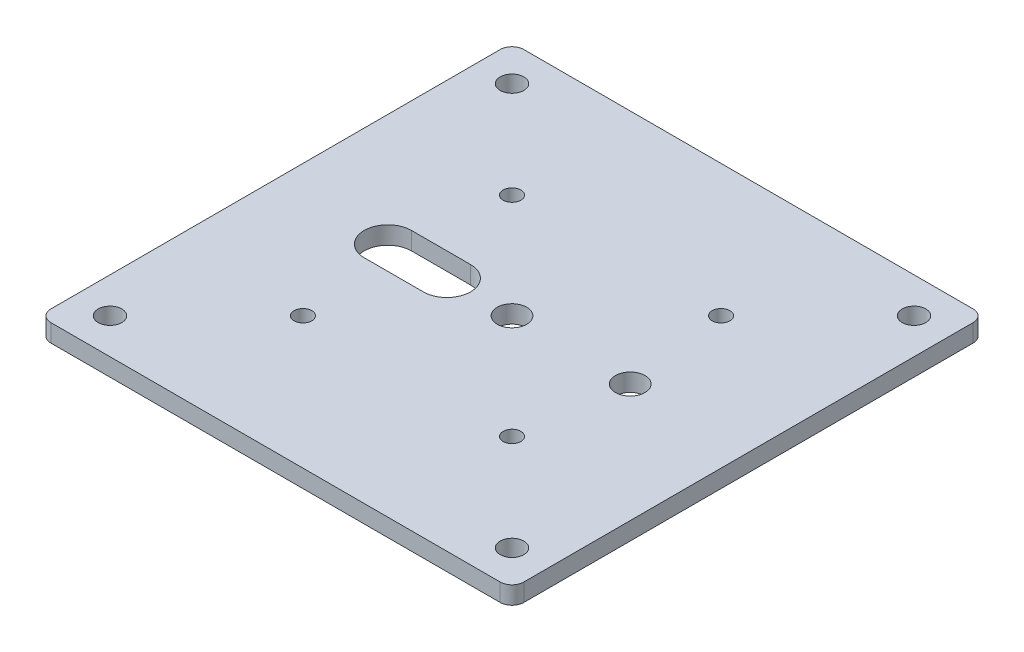
SolidWorks part; units mm, degrees
ref_plane "Face" through (0, 0, 0) normal (0, 0, 1) x (1, 0, 0)
ref_plane "Dessus" through (0, 0, 0) normal (0, 1, 0) x (1, 0, 0)
ref_plane "Droite" through (0, 0, 0) normal (1, 0, 0) x (0, 0, -1)
sketch "Esquisse1" plane through (0, 0, 0) normal (0, 1, 0) x (1, 0, 0)
  line L0 (0, 40) -> (80, 40) construction
  line L1 (0, 0) -> (80, 0)
  line L2 (0, 0) -> (0, 80)
  line L3 (0, 80) -> (80, 80)
  line L4 (80, 0) -> (80, 80)
  line L5 (40, 80) -> (40, 0) construction
  line L6 (0, 0) -> (80, 80) construction
  line L7 (0, 80) -> (80, 0) construction
  line L8 (19, 44) -> (29, 44)
  line L9 (19, 36) -> (29, 36)
  circle A0 centre (40, 40) radius 2.5
  circle A1 centre (60, 40) radius 2.5
  circle A2 centre (57.6777, 57.6777) radius 1.5
  circle A3 centre (22.3223, 22.3223) radius 1.5
  circle A4 centre (22.3223, 57.6777) radius 1.5
  circle A5 centre (57.6777, 22.3223) radius 1.5
  arc A6 (19, 44) -> (15, 40) centre (19, 40) ccw
  arc A7 (29, 44) -> (33, 40) centre (29, 40) cw
  arc A8 (29, 36) -> (33, 40) centre (29, 40) ccw
  arc A9 (19, 36) -> (15, 40) centre (19, 40) cw
  circle A10 centre (6, 74) radius 2
  circle A11 centre (74, 74) radius 2
  circle A12 centre (74, 6) radius 2
  circle A13 centre (6, 6) radius 2
  dimension "D2" = 5
  dimension "D4" = 3
  dimension "D5" = 25
  dimension "D10" = 4
  dimension "D1" = 80
  dimension "D3" = 20
  dimension "D6" = 25
  dimension "D7" = 8
  dimension "D8" = 10
  dimension "D9" = 15
  dimension "D11" = 6
extrude "Extrusion1" add sketch "Esquisse1" along normal blind 3
fillet "Congé1" radius 2 4 edges at (80, 1.5, -80) (80, 1.5, 0) (0, 1.5, -80) (0, 1.5, 0)
